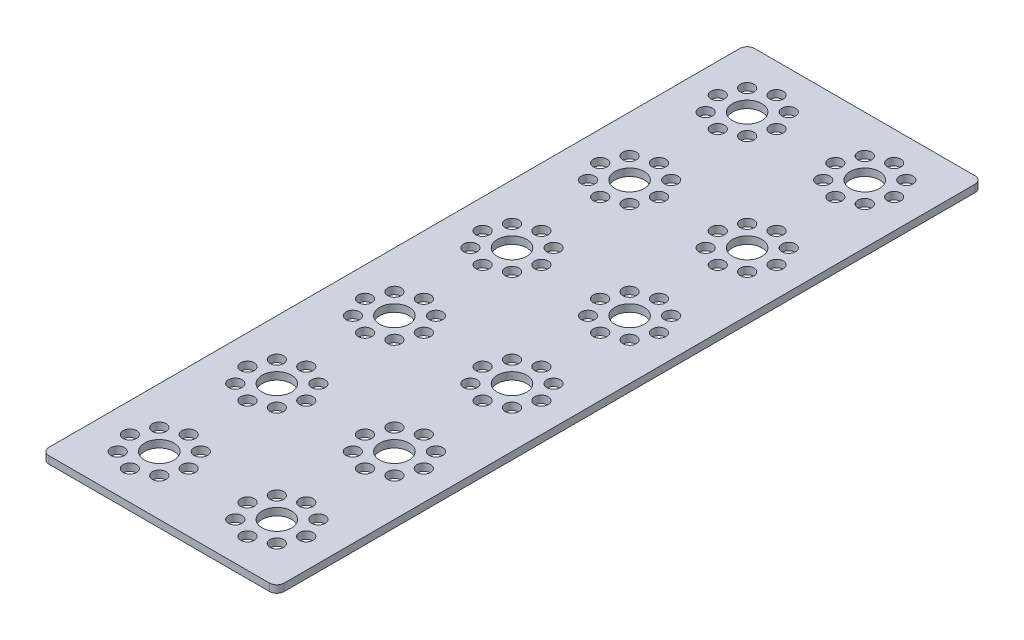
SolidWorks part; units mm, degrees
material "2024 Alloy"
ref_plane "Front Plane" through (0, 0, 0) normal (0, 0, 1) x (1, 0, 0)
ref_plane "Top Plane" through (0, 0, 0) normal (0, 1, 0) x (1, 0, 0)
ref_plane "Right Plane" through (0, 0, 0) normal (1, 0, 0) x (0, 0, -1)
ref_plane "Plane1" through (0, 0, 0) normal (0, -1, 0) x (1, 0, 0)
sketch "Sketch1" plane through (0, 0, 0) normal (0, -1, 0) x (1, 0, 0)
  line L0 (48, -174) -> (48, 14)
  line L1 (46, 16) -> (-14, 16)
  line L2 (-16, 14) -> (-16, -174)
  line L3 (-14, -176) -> (46, -176)
  circle A0 centre (37.6569, -154.3431) radius 1.85
  circle A1 centre (26.3431, -154.3431) radius 1.85
  circle A2 centre (26.3431, -165.6569) radius 1.85
  circle A3 centre (37.6569, -165.6569) radius 1.85
  circle A4 centre (24, -160) radius 1.85
  circle A5 centre (32, -152) radius 1.85
  circle A6 centre (40, -160) radius 1.85
  circle A7 centre (32, -168) radius 1.85
  circle A8 centre (32, -160) radius 4
  circle A9 centre (5.6569, -154.3431) radius 1.85
  circle A10 centre (-5.6569, -154.3431) radius 1.85
  circle A11 centre (-5.6569, -165.6569) radius 1.85
  circle A12 centre (5.6569, -165.6569) radius 1.85
  circle A13 centre (-8, -160) radius 1.85
  circle A14 centre (0, -152) radius 1.85
  circle A15 centre (8, -160) radius 1.85
  circle A16 centre (0, -168) radius 1.85
  circle A17 centre (0, -160) radius 4
  circle A18 centre (37.6569, -122.3431) radius 1.85
  circle A19 centre (26.3431, -122.3431) radius 1.85
  circle A20 centre (26.3431, -133.6569) radius 1.85
  circle A21 centre (37.6569, -133.6569) radius 1.85
  circle A22 centre (24, -128) radius 1.85
  circle A23 centre (32, -120) radius 1.85
  circle A24 centre (40, -128) radius 1.85
  circle A25 centre (32, -136) radius 1.85
  circle A26 centre (32, -128) radius 4
  circle A27 centre (5.6569, -122.3431) radius 1.85
  circle A28 centre (-5.6569, -122.3431) radius 1.85
  circle A29 centre (-5.6569, -133.6569) radius 1.85
  circle A30 centre (5.6569, -133.6569) radius 1.85
  circle A31 centre (-8, -128) radius 1.85
  circle A32 centre (0, -120) radius 1.85
  circle A33 centre (8, -128) radius 1.85
  circle A34 centre (0, -136) radius 1.85
  circle A35 centre (0, -128) radius 4
  circle A36 centre (37.6569, -90.3431) radius 1.85
  circle A37 centre (26.3431, -90.3431) radius 1.85
  circle A38 centre (26.3431, -101.6569) radius 1.85
  circle A39 centre (37.6569, -101.6569) radius 1.85
  circle A40 centre (24, -96) radius 1.85
  circle A41 centre (32, -88) radius 1.85
  circle A42 centre (40, -96) radius 1.85
  circle A43 centre (32, -104) radius 1.85
  circle A44 centre (32, -96) radius 4
  circle A45 centre (5.6569, -90.3431) radius 1.85
  circle A46 centre (-5.6569, -90.3431) radius 1.85
  circle A47 centre (-5.6569, -101.6569) radius 1.85
  circle A48 centre (5.6569, -101.6569) radius 1.85
  circle A49 centre (-8, -96) radius 1.85
  circle A50 centre (0, -88) radius 1.85
  circle A51 centre (8, -96) radius 1.85
  circle A52 centre (0, -104) radius 1.85
  circle A53 centre (0, -96) radius 4
  circle A54 centre (37.6569, -58.3431) radius 1.85
  circle A55 centre (26.3431, -58.3431) radius 1.85
  circle A56 centre (26.3431, -69.6569) radius 1.85
  circle A57 centre (37.6569, -69.6569) radius 1.85
  circle A58 centre (24, -64) radius 1.85
  circle A59 centre (32, -56) radius 1.85
  circle A60 centre (40, -64) radius 1.85
  circle A61 centre (32, -72) radius 1.85
  circle A62 centre (32, -64) radius 4
  circle A63 centre (5.6569, -58.3431) radius 1.85
  circle A64 centre (-5.6569, -58.3431) radius 1.85
  circle A65 centre (-5.6569, -69.6569) radius 1.85
  circle A66 centre (5.6569, -69.6569) radius 1.85
  circle A67 centre (-8, -64) radius 1.85
  circle A68 centre (0, -56) radius 1.85
  circle A69 centre (8, -64) radius 1.85
  circle A70 centre (0, -72) radius 1.85
  circle A71 centre (0, -64) radius 4
  circle A72 centre (0, 0) radius 4
  circle A73 centre (37.6569, -26.3431) radius 1.85
  circle A74 centre (26.3431, -26.3431) radius 1.85
  circle A75 centre (26.3431, -37.6569) radius 1.85
  circle A76 centre (37.6569, -37.6569) radius 1.85
  circle A77 centre (24, -32) radius 1.85
  circle A78 centre (32, -24) radius 1.85
  circle A79 centre (40, -32) radius 1.85
  circle A80 centre (32, -40) radius 1.85
  circle A81 centre (32, -32) radius 4
  circle A82 centre (5.6569, -26.3431) radius 1.85
  circle A83 centre (-5.6569, -26.3431) radius 1.85
  circle A84 centre (-5.6569, -37.6569) radius 1.85
  circle A85 centre (5.6569, -37.6569) radius 1.85
  circle A86 centre (-8, -32) radius 1.85
  circle A87 centre (0, -24) radius 1.85
  circle A88 centre (8, -32) radius 1.85
  circle A89 centre (0, -40) radius 1.85
  circle A90 centre (0, -32) radius 4
  circle A91 centre (37.6569, 5.6569) radius 1.85
  circle A92 centre (26.3431, 5.6569) radius 1.85
  circle A93 centre (26.3431, -5.6569) radius 1.85
  circle A94 centre (37.6569, -5.6569) radius 1.85
  circle A95 centre (24, 0) radius 1.85
  circle A96 centre (32, 8) radius 1.85
  circle A97 centre (40, 0) radius 1.85
  circle A98 centre (32, -8) radius 1.85
  circle A99 centre (32, 0) radius 4
  circle A100 centre (5.6569, 5.6569) radius 1.85
  circle A101 centre (-5.6569, 5.6569) radius 1.85
  circle A102 centre (-5.6569, -5.6569) radius 1.85
  circle A103 centre (5.6569, -5.6569) radius 1.85
  circle A104 centre (-8, 0) radius 1.85
  circle A105 centre (0, 8) radius 1.85
  circle A106 centre (8, 0) radius 1.85
  circle A107 centre (0, -8) radius 1.85
  arc A108 (46, -176) -> (48, -174) centre (46, -174) ccw
  arc A109 (48, 14) -> (46, 16) centre (46, 14) ccw
  arc A110 (-14, 16) -> (-16, 14) centre (-14, 14) ccw
  arc A111 (-16, -174) -> (-14, -176) centre (-14, -174) ccw
extrude "Boss-Extrude1" add sketch "Sketch1" against normal blind 2
